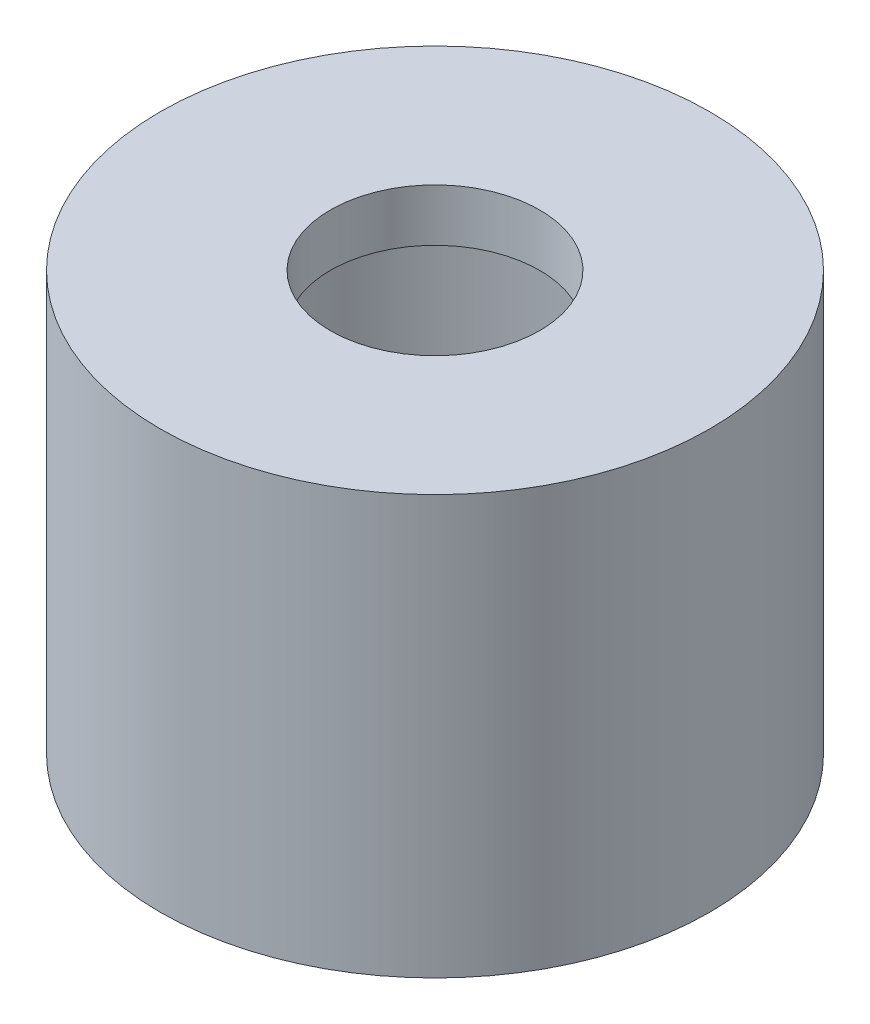
SolidWorks part; units mm, degrees
ref_plane "Plan de face" through (0, 0, 0) normal (0, 0, 1) x (1, 0, 0)
ref_plane "Plan de dessus" through (0, 0, 0) normal (0, 1, 0) x (1, 0, 0)
ref_plane "Plan de droite" through (0, 0, 0) normal (1, 0, 0) x (0, 0, -1)
sketch "Esquisse1" plane through (0, 0, 0) normal (0, 0, 1) x (1, 0, 0)
  line L1 (-10.5, -3) -> (-4, -3)
  line L2 (-10.5, -19) -> (-8.5, -19)
  line L3 (-10.5, -3) -> (-10.5, -19)
  line L4 (-4, -3) -> (-4, -5)
  line L5 (-8.5, -5) -> (-4, -5)
  line L6 (0, 0) -> (0, -6.1839) construction
  line L7 (-8.5, -3) -> (-4, -3) construction
  line L8 (-8.5, -5) -> (-8.5, -19)
  line L9 (-8.5, 0) -> (-8.5, -6.1839) construction
revolve "Révolution1" add sketch "Esquisse1" angle 360 about L6
